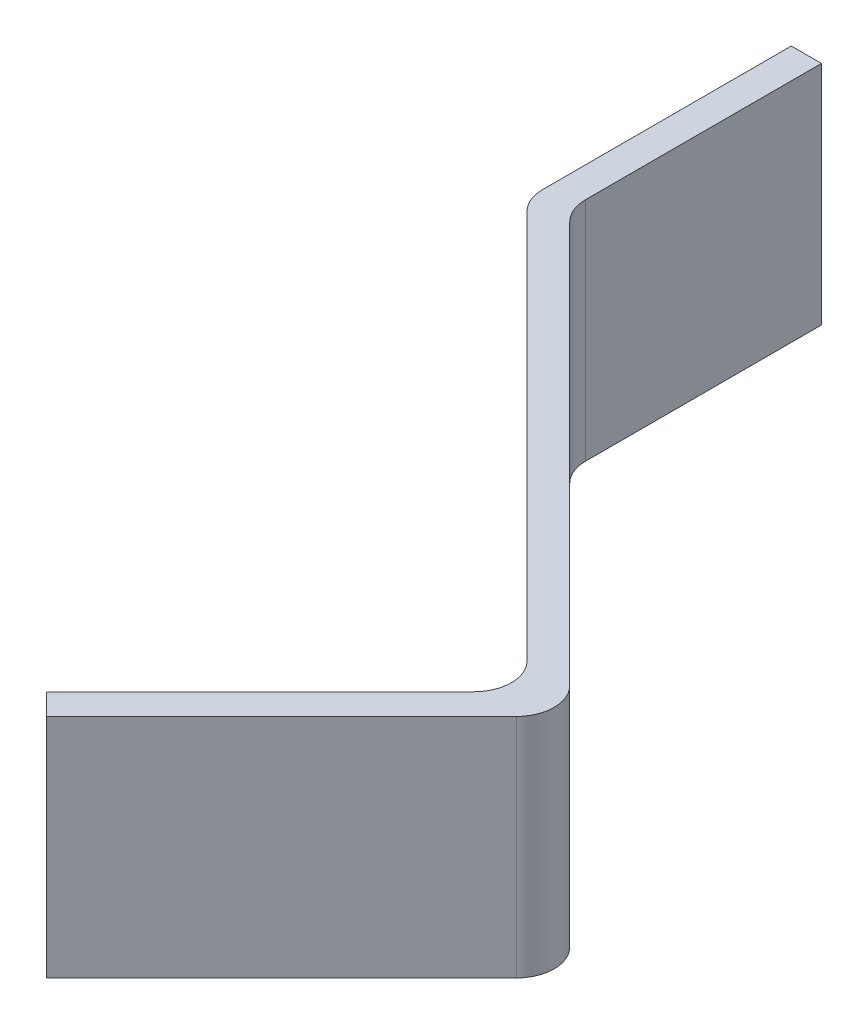
SolidWorks part; units mm, degrees
ref_plane "Front Plane" through (0, 0, 0) normal (0, 0, 1) x (1, 0, 0)
ref_plane "Top Plane" through (0, 0, 0) normal (0, 1, 0) x (1, 0, 0)
ref_plane "Right Plane" through (0, 0, 0) normal (1, 0, 0) x (0, 0, -1)
ref_plane "Plane1" through (0, 7.5, 0) normal (0, 1, 0) x (1, 0, 0)
sketch "Sketch1" plane through (0, 7.5, 0) normal (0, 1, 0) x (1, 0, 0)
  line B0 (248.7921, 5.1767) -> (195.5667, 58.4021)
  line B1 (194.1023, 61.9376) -> (194.1023, 93.2097)
  line B2 (194.1023, 93.2097) -> (190.1023, 93.2097)
  line B3 (190.1023, 93.2097) -> (190.1023, 60.2807)
  line B4 (191.5667, 56.7452) -> (243.1353, 5.1767)
  line B5 (243.1353, -1.8944) -> (214.851, -30.1787)
  line B6 (214.851, -30.1787) -> (217.6794, -33.0071)
  line B7 (217.6794, -33.0071) -> (248.7921, -1.8944)
  arc B8 (248.7921, -1.8944) -> (248.7921, 5.1767) centre (245.2566, 1.6411) ccw
  arc B9 (194.1023, 61.9376) -> (195.5667, 58.4021) centre (199.1023, 61.9376) ccw
  arc B10 (190.1023, 60.2807) -> (191.5667, 56.7452) centre (195.1023, 60.2807) ccw
  arc B11 (243.1353, -1.8944) -> (243.1353, 5.1767) centre (239.5997, 1.6411) ccw
sketch_block_instance "Block1-1"
sketch_block "Block1"
extrude "Boss-Extrude1" add sketch "Sketch1" against normal blind 30
